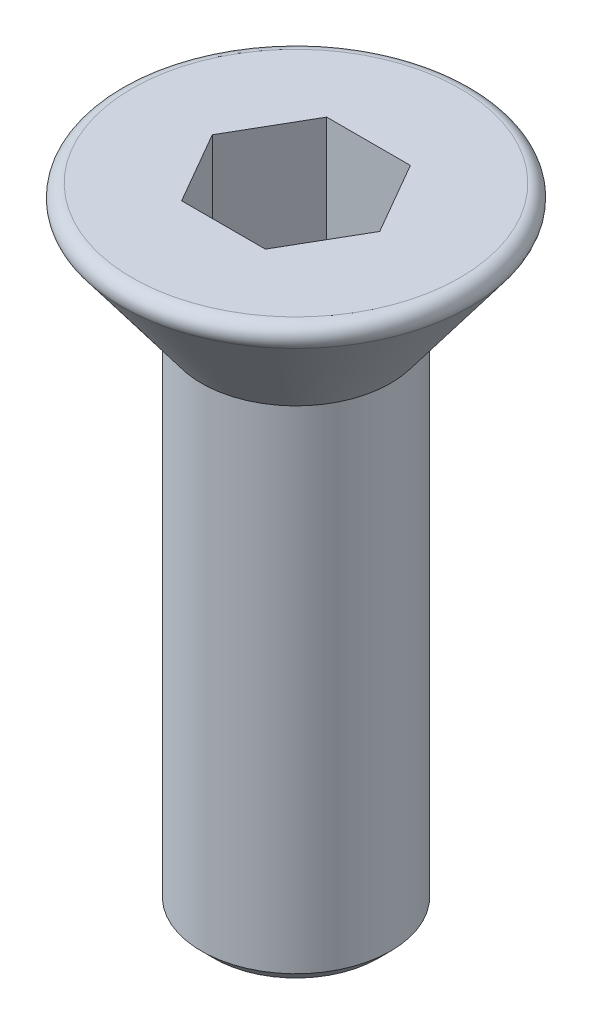
SolidWorks part; units mm, degrees
ref_plane "前视" through (0, 0, 0) normal (0, 0, 1) x (1, 0, 0)
ref_plane "上视" through (0, 0, 0) normal (0, 1, 0) x (1, 0, 0)
ref_plane "右视" through (0, 0, 0) normal (1, 0, 0) x (0, 0, -1)
sketch "草图1" plane through (0, 0, 0) normal (0, 0, 1) x (1, 0, 0)
  line L0 (0, 0) -> (0, -2)
  line L1 (0, -2) -> (1.5, -2)
  line L2 (3, 0) -> (0, 0)
  line L3 (1.5, -2) -> (3, 0)
  dimension "D1" = 3
  dimension "D2" = 1.5
  dimension "D3" = 2
revolve "旋转1" add sketch "草图1" angle 360 about L0
sketch "草图2" plane through (0, -2, 0) normal (0, -1, 0) x (1, 0, 0)
  circle A0 centre (0, 0) radius 1.5
extrude "凸台-拉伸1" add sketch "草图2" along normal blind 8
sketch "草图3" plane through (0, 0, 0) normal (0, 1, 0) x (1, 0, 0)
  line L1 (-1.3279, 0) -> (-0.664, -1.15)
  line L2 (-0.664, -1.15) -> (0.664, -1.15)
  line L3 (0.664, -1.15) -> (1.3279, 0)
  line L4 (1.3279, 0) -> (0.664, 1.15)
  line L5 (0.664, 1.15) -> (-0.664, 1.15)
  line L6 (-0.664, 1.15) -> (-1.3279, 0)
  circle A0 centre (0, 0) radius 1.15 construction
  dimension "D1" = 2.3
extrude "切除-拉伸1" cut sketch "草图3" against normal blind 2
chamfer "倒角1" distance 0.2 angle 45 1 edges at (1.5, -10, 0)
fillet "圆角1" radius 0.2 1 edges at (-3, 0, 0)
